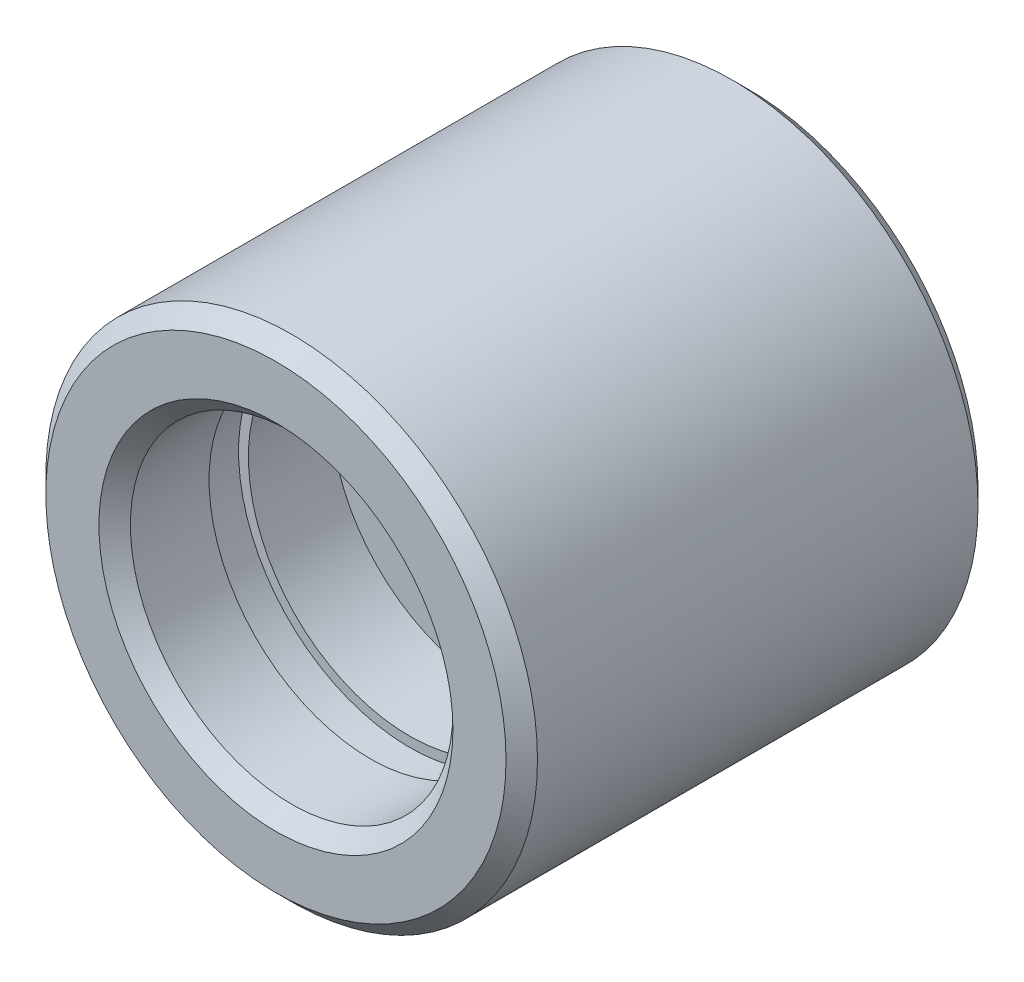
SolidWorks part; units mm, degrees
ref_plane "Front Plane" through (0, 0, 0) normal (0, 0, 1) x (1, 0, 0)
ref_plane "Top Plane" through (0, 0, 0) normal (0, 1, 0) x (1, 0, 0)
ref_plane "Right Plane" through (0, 0, 0) normal (1, 0, 0) x (0, 0, -1)
sketch "Sketch1" plane through (0, 0, 0) normal (0, 0, 1) x (1, 0, 0)
  circle A0 centre (0, 0) radius 6.25
  dimension "D1" = 12.5
extrude "Boss-Extrude1" add sketch "Sketch1" along normal blind 12
sketch "Sketch2" plane through (0, 0, 12) normal (0, 0, 1) x (1, 0, 0)
  circle A0 centre (0, 0) radius 1.5
  dimension "D1" = 3
extrude "Cut-Extrude1" cut sketch "Sketch2" against normal up to next
sketch "Sketch3" plane through (0, 0, 12) normal (0, 0, 1) x (1, 0, 0)
  circle A0 centre (0, 0) radius 4.1
  dimension "D1" = 8.2
extrude "Cut-Extrude2" cut sketch "Sketch3" against normal blind 5.5
sketch "Sketch4" plane through (0, 0, 0) normal (0, 0, -1) x (-1, 0, 0)
  circle A0 centre (0, 0) radius 4.1
  dimension "D1" = 8.2
extrude "Cut-Extrude3" cut sketch "Sketch4" against normal blind 5.5
sketch "Sketch5" plane through (0, 0, 0) normal (0, 1, 0) x (1, 0, 0)
  line L0 (-4.1, -12) -> (4.1, -12) construction
  line L1 (4.1, 0) -> (-4.1, 0) construction
  line L2 (-4.1, -12) -> (4.1, -12) construction
  line L3 (4.1, 0) -> (-4.1, 0) construction
  line L5 (4.1, -2.4) -> (4.35, -2.4)
  line L6 (4.1, -2.4) -> (4.1, -3.4)
  line L7 (4.1, -3.4) -> (4.35, -3.4)
  line L8 (4.35, -2.4) -> (4.35, -3.4)
  line L9 (4.1, -9.6) -> (4.35, -9.6)
  line L10 (4.1, -9.6) -> (4.1, -8.6)
  line L11 (4.1, -8.6) -> (4.35, -8.6)
  line L12 (4.35, -9.6) -> (4.35, -8.6)
  dimension "D1" = 1
  dimension "D2" = 0.25
  dimension "D3" = 1
  dimension "D4" = 0.25
  dimension "D5" = 2.4
  dimension "D6" = 2.4
ref_axis "Axis1" through (0, 0, 12) along (0, 0, -1)
revolve "Cut-Revolve1" cut sketch "Sketch5" angle 360 about axis through (0, 0, 12) along (0, 0, -1)
sketch "Sketch6" plane through (0, 0, 5.5) normal (0, 0, -1) x (-1, 0, 0)
  line L0 (-3.8158, -1.5) -> (3.8158, -1.5)
  line L1 (-3.8158, 1.5) -> (3.8158, 1.5)
  circle A0 centre (0, 0) radius 4.1 construction
  circle A1 centre (0, 0) radius 1.5 construction
  circle A2 centre (0, 0) radius 4.1
  circle M3 centre (0, 0) radius 4.1
  circle M4 centre (0, 0) radius 1.5
extrude "Cut-Extrude4" cut sketch "Sketch6" against normal blind 0.4 contours L1 L0 M3 M4 | L1 L0 M4 M3
sketch "Sketch7" plane through (0, 0, 5.9) normal (0, 0, -1) x (-1, 0, 0)
  line L0 (3.8158, 1.5) -> (0, 1.5) construction
  line L1 (0, -1.5) -> (3.8158, -1.5) construction
  line L2 (0, 1.5) -> (-3.8158, 1.5) construction
  line L3 (-3.8158, -1.5) -> (0, -1.5) construction
  line L4 (3.8158, 1.5) -> (0, 1.5)
  line L5 (0, -1.5) -> (3.8158, -1.5)
  line L6 (0, 1.5) -> (-3.8158, 1.5)
  line L7 (-3.8158, -1.5) -> (0, -1.5)
  line L8 (-1.5, -1.5) -> (-1.5, 1.5)
  line L9 (1.5, 1.5) -> (1.5, -1.5)
  arc A0 (0, -1.5) -> (0, 1.5) centre (0, 0) ccw construction
  arc A1 (3.8158, -1.5) -> (3.8158, 1.5) centre (0, 0) ccw construction
  arc A2 (-3.8158, 1.5) -> (-3.8158, -1.5) centre (0, 0) ccw construction
  arc A3 (0, 1.5) -> (0, -1.5) centre (0, 0) ccw construction
  arc A4 (0, -1.5) -> (0, 1.5) centre (0, 0) ccw
  arc A5 (3.8158, -1.5) -> (3.8158, 1.5) centre (0, 0) ccw
  arc A6 (-3.8158, 1.5) -> (-3.8158, -1.5) centre (0, 0) ccw
  arc A7 (0, 1.5) -> (0, -1.5) centre (0, 0) ccw
  arc M4 (-3.8158, 1.5) -> (-3.8158, -1.5) centre (0, 0) ccw
  line M5 (-3.8158, -1.5) -> (0, -1.5)
extrude "Boss-Extrude2" add sketch "Sketch7" along normal blind 0.2 contours L8 L6 M5 M4 | L5 A5 L4 L9
ref_point "Point2"
chamfer "Chamfer1" distance 0.4 angle 45 4 edges at (6.25, 0, 12) (4.1, 0, 12) (6.25, 0, 0) (-4.1, 0, 0)
